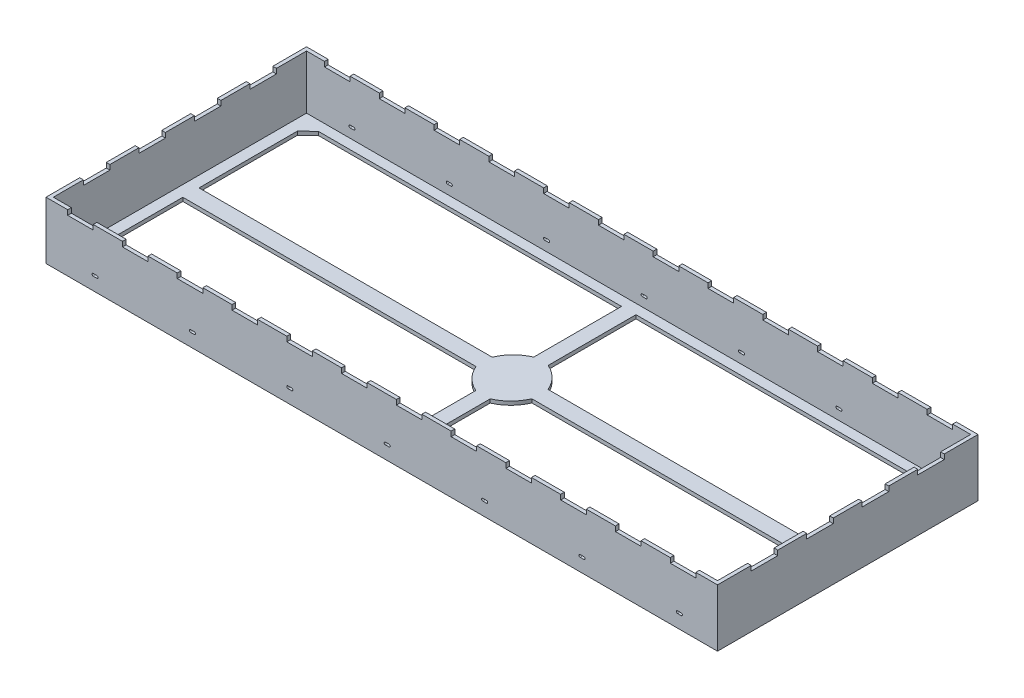
SolidWorks part; units mm, degrees
ref_plane "Front Plane" through (0, 0, 0) normal (0, 0, 1) x (1, 0, 0)
ref_plane "Top Plane" through (0, 0, 0) normal (0, 1, 0) x (1, 0, 0)
ref_plane "Right Plane" through (0, 0, 0) normal (1, 0, 0) x (0, 0, -1)
sketch "Sketch1" plane through (0, 0, 0) normal (0, 1, 0) x (1, 0, 0)
  line L1 (-35.0266, 13.589) -> (35.0266, 13.589)
  line L2 (-35.0266, 13.589) -> (-35.0266, -13.589)
  line L3 (-35.0266, -13.589) -> (35.0266, -13.589)
  line L4 (35.0266, 13.589) -> (35.0266, -13.589)
  line L5 (-35.0266, 13.589) -> (35.0266, -13.589) construction
  line L6 (-35.0266, -13.589) -> (35.0266, 13.589) construction
  point P0 (0, 0)
  dimension "D1" = 70.0532
  dimension "D2" = 27.178
extrude "Boss-Extrude1" add sketch "Sketch1" along normal blind 5.9944
shell "Shell1" thickness 0.381
sketch "Sketch2" plane through (0, 0, 0) normal (0, -1, 0) x (1, 0, 0)
  line L0 (131.1471, 197.1305) -> (804.4804, 197.1305) construction
  line L1 (-32.38, 12.1805) -> (-0.7521, 12.1805)
  line L2 (-0.7521, 12.1805) -> (-0.7521, 3.0227)
  line L3 (-32.38, 12.1805) -> (-33.4968, 11.1083)
  line L4 (-33.4968, 11.1083) -> (-33.4968, 0.844)
  line L5 (-33.4968, 0.844) -> (-2.9133, 0.844)
  line L6 (0, 13.589) -> (0, -13.589) construction
  line L7 (-35.0266, 13.589) -> (35.0266, 13.589) construction
  line L8 (35.0266, -13.589) -> (-35.0266, -13.589) construction
  line L9 (33.4968, 0.844) -> (2.9133, 0.844)
  line L10 (33.4968, 11.1083) -> (33.4968, 0.844)
  line L11 (32.38, 12.1805) -> (33.4968, 11.1083)
  line L12 (0.7521, 12.1805) -> (0.7521, 3.0227)
  line L13 (32.38, 12.1805) -> (0.7521, 12.1805)
  line L14 (-35.0266, 0) -> (35.0266, 0) construction
  line L15 (-35.0266, -13.589) -> (-35.0266, 13.589) construction
  line L16 (35.0266, 13.589) -> (35.0266, -13.589) construction
  line L17 (32.38, -12.1805) -> (0.7521, -12.1805)
  line L18 (0.7521, -12.1805) -> (0.7521, -3.0227)
  line L19 (32.38, -12.1805) -> (33.4968, -11.1083)
  line L20 (33.4968, -11.1083) -> (33.4968, -0.844)
  line L21 (33.4968, -0.844) -> (2.9133, -0.844)
  line L22 (-33.4968, -0.844) -> (-2.9133, -0.844)
  line L23 (-33.4968, -11.1083) -> (-33.4968, -0.844)
  line L24 (-32.38, -12.1805) -> (-33.4968, -11.1083)
  line L25 (-0.7521, -12.1805) -> (-0.7521, -3.0227)
  line L26 (-32.38, -12.1805) -> (-0.7521, -12.1805)
  arc A0 (-0.7521, 3.0227) -> (-2.9133, 0.844) centre (0.9215, -0.7987) ccw
  arc A1 (0.7521, 3.0227) -> (2.9133, 0.844) centre (-0.9215, -0.7987) cw
  arc A2 (0.7521, -3.0227) -> (2.9133, -0.844) centre (-0.9215, 0.7987) ccw
  arc A3 (-0.7521, -3.0227) -> (-2.9133, -0.844) centre (0.9215, 0.7987) cw
extrude "Cut-Extrude1" cut sketch "Sketch2" against normal through all
sketch "Sketch3" plane through (0, 0, -13.589) normal (0, 0, -1) x (-1, 0, 0)
  line L0 (-35.0266, 5.9944) -> (35.0266, 5.9944) construction
  line L1 (-32.766, 6.8594) -> (-30.099, 6.8594)
  line L2 (-32.766, 6.8594) -> (-32.766, 5.4864)
  line L3 (-32.766, 5.4864) -> (-30.099, 5.4864)
  line L4 (-30.099, 6.8594) -> (-30.099, 5.4864)
  line L6 (-27.051, 6.8594) -> (-24.384, 6.8594)
  line L7 (-27.051, 6.8594) -> (-27.051, 5.4864)
  line L8 (-27.051, 5.4864) -> (-24.384, 5.4864)
  line L9 (-24.384, 6.8594) -> (-24.384, 5.4864)
  line L10 (-21.336, 6.8594) -> (-18.669, 6.8594)
  line L11 (-21.336, 6.8594) -> (-21.336, 5.4864)
  line L12 (-21.336, 5.4864) -> (-18.669, 5.4864)
  line L13 (-18.669, 6.8594) -> (-18.669, 5.4864)
  line L14 (-15.621, 6.8594) -> (-12.954, 6.8594)
  line L15 (-15.621, 6.8594) -> (-15.621, 5.4864)
  line L16 (-15.621, 5.4864) -> (-12.954, 5.4864)
  line L17 (-12.954, 6.8594) -> (-12.954, 5.4864)
  line L18 (-9.906, 6.8594) -> (-7.239, 6.8594)
  line L19 (-9.906, 6.8594) -> (-9.906, 5.4864)
  line L20 (-9.906, 5.4864) -> (-7.239, 5.4864)
  line L21 (-7.239, 6.8594) -> (-7.239, 5.4864)
  line L22 (-4.191, 6.8594) -> (-1.524, 6.8594)
  line L23 (-4.191, 6.8594) -> (-4.191, 5.4864)
  line L24 (-4.191, 5.4864) -> (-1.524, 5.4864)
  line L25 (-1.524, 6.8594) -> (-1.524, 5.4864)
  line L26 (1.524, 6.8594) -> (4.191, 6.8594)
  line L27 (1.524, 6.8594) -> (1.524, 5.4864)
  line L28 (1.524, 5.4864) -> (4.191, 5.4864)
  line L29 (4.191, 6.8594) -> (4.191, 5.4864)
  line L30 (7.239, 6.8594) -> (9.906, 6.8594)
  line L31 (7.239, 6.8594) -> (7.239, 5.4864)
  line L32 (7.239, 5.4864) -> (9.906, 5.4864)
  line L33 (9.906, 6.8594) -> (9.906, 5.4864)
  line L34 (12.954, 6.8594) -> (15.621, 6.8594)
  line L35 (12.954, 6.8594) -> (12.954, 5.4864)
  line L36 (12.954, 5.4864) -> (15.621, 5.4864)
  line L37 (15.621, 6.8594) -> (15.621, 5.4864)
  line L38 (18.669, 6.8594) -> (21.336, 6.8594)
  line L39 (18.669, 6.8594) -> (18.669, 5.4864)
  line L40 (18.669, 5.4864) -> (21.336, 5.4864)
  line L41 (21.336, 6.8594) -> (21.336, 5.4864)
  line L42 (24.384, 6.8594) -> (27.051, 6.8594)
  line L43 (24.384, 6.8594) -> (24.384, 5.4864)
  line L44 (24.384, 5.4864) -> (27.051, 5.4864)
  line L45 (27.051, 6.8594) -> (27.051, 5.4864)
  line L46 (30.099, 6.8594) -> (32.766, 6.8594)
  line L47 (30.099, 6.8594) -> (30.099, 5.4864)
  line L48 (30.099, 5.4864) -> (32.766, 5.4864)
  line L49 (32.766, 6.8594) -> (32.766, 5.4864)
  line L50 (-32.766, 6.8594) -> (-27.051, 6.8594) construction
  line L53 (-35.0266, 5.9944) -> (-32.766, 6.8594) construction
  line L54 (32.766, 6.8594) -> (35.0266, 5.9944) construction
  dimension "D1" = 2.667
  dimension "D2" = 0.508
  dimension "D5" = 3.048
  dimension "D4" = 12
extrude "Cut-Extrude2" cut sketch "Sketch3" against normal through all
sketch "Sketch4" plane through (35.0266, 0, 0) normal (1, 0, 0) x (0, 0, -1)
  line L0 (-13.589, 5.9944) -> (13.589, 5.9944) construction
  line L1 (-10.0711, 7.1888) -> (-7.3025, 7.1888)
  line L2 (-10.0711, 7.1888) -> (-10.0711, 5.4864)
  line L3 (-10.0711, 5.4864) -> (-7.3025, 5.4864)
  line L4 (-7.3025, 7.1888) -> (-7.3025, 5.4864)
  line L5 (-4.2799, 7.1888) -> (-1.5113, 7.1888)
  line L6 (-4.2799, 7.1888) -> (-4.2799, 5.4864)
  line L7 (-4.2799, 5.4864) -> (-1.5113, 5.4864)
  line L8 (-1.5113, 7.1888) -> (-1.5113, 5.4864)
  line L9 (1.5113, 7.1888) -> (4.2799, 7.1888)
  line L10 (1.5113, 7.1888) -> (1.5113, 5.4864)
  line L11 (1.5113, 5.4864) -> (4.2799, 5.4864)
  line L12 (4.2799, 7.1888) -> (4.2799, 5.4864)
  line L13 (7.3025, 7.1888) -> (10.0711, 7.1888)
  line L14 (7.3025, 7.1888) -> (7.3025, 5.4864)
  line L15 (7.3025, 5.4864) -> (10.0711, 5.4864)
  line L16 (10.0711, 7.1888) -> (10.0711, 5.4864)
  line L17 (-10.0711, 7.1888) -> (-4.2799, 7.1888) construction
  line L18 (-10.0711, 7.1888) -> (-13.589, 5.9944) construction
  line L19 (10.0711, 7.1888) -> (13.589, 5.9944) construction
  line L20 (13.589, 5.9944) -> (13.589, 0) construction
  dimension "D1" = 2.7686
  dimension "D2" = 0.508
  dimension "D4" = 3.0226
  dimension "D3" = 4
extrude "Cut-Extrude3" cut sketch "Sketch4" against normal through all
sketch "Sketch5" plane through (0, 0, -13.589) normal (0, 0, -1) x (-1, 0, 0)
  line L0 (-31.242, 1.4478) -> (-30.861, 1.4478) construction
  line L1 (-31.242, 1.5748) -> (-30.861, 1.5748)
  line L2 (-31.242, 1.3208) -> (-30.861, 1.3208)
  line L4 (-35.0266, 0) -> (35.0266, 0) construction
  line L5 (-21.082, 1.4478) -> (-20.701, 1.4478) construction
  line L6 (-21.082, 1.5748) -> (-20.701, 1.5748)
  line L7 (-21.082, 1.3208) -> (-20.701, 1.3208)
  line L8 (-10.922, 1.4478) -> (-10.541, 1.4478) construction
  line L9 (-10.922, 1.5748) -> (-10.541, 1.5748)
  line L10 (-10.922, 1.3208) -> (-10.541, 1.3208)
  line L11 (-0.762, 1.4478) -> (-0.381, 1.4478) construction
  line L12 (-0.762, 1.5748) -> (-0.381, 1.5748)
  line L13 (-0.762, 1.3208) -> (-0.381, 1.3208)
  line L14 (9.398, 1.4478) -> (9.779, 1.4478) construction
  line L15 (9.398, 1.5748) -> (9.779, 1.5748)
  line L16 (9.398, 1.3208) -> (9.779, 1.3208)
  line L17 (19.558, 1.4478) -> (19.939, 1.4478) construction
  line L18 (19.558, 1.5748) -> (19.939, 1.5748)
  line L19 (19.558, 1.3208) -> (19.939, 1.3208)
  line L20 (29.718, 1.4478) -> (30.099, 1.4478) construction
  line L21 (29.718, 1.5748) -> (30.099, 1.5748)
  line L22 (29.718, 1.3208) -> (30.099, 1.3208)
  line L23 (-31.242, 1.4478) -> (-21.082, 1.4478) construction
  line L24 (-35.0266, 5.9944) -> (-35.0266, 0) construction
  arc A0 (-31.242, 1.5748) -> (-31.242, 1.3208) centre (-31.242, 1.4478) ccw
  arc A1 (-30.861, 1.3208) -> (-30.861, 1.5748) centre (-30.861, 1.4478) ccw
  arc A2 (-21.082, 1.5748) -> (-21.082, 1.3208) centre (-21.082, 1.4478) ccw
  arc A3 (-20.701, 1.3208) -> (-20.701, 1.5748) centre (-20.701, 1.4478) ccw
  arc A4 (-10.922, 1.5748) -> (-10.922, 1.3208) centre (-10.922, 1.4478) ccw
  arc A5 (-10.541, 1.3208) -> (-10.541, 1.5748) centre (-10.541, 1.4478) ccw
  arc A6 (-0.762, 1.5748) -> (-0.762, 1.3208) centre (-0.762, 1.4478) ccw
  arc A7 (-0.381, 1.3208) -> (-0.381, 1.5748) centre (-0.381, 1.4478) ccw
  arc A8 (9.398, 1.5748) -> (9.398, 1.3208) centre (9.398, 1.4478) ccw
  arc A9 (9.779, 1.3208) -> (9.779, 1.5748) centre (9.779, 1.4478) ccw
  arc A10 (19.558, 1.5748) -> (19.558, 1.3208) centre (19.558, 1.4478) ccw
  arc A11 (19.939, 1.3208) -> (19.939, 1.5748) centre (19.939, 1.4478) ccw
  arc A12 (29.718, 1.5748) -> (29.718, 1.3208) centre (29.718, 1.4478) ccw
  arc A13 (30.099, 1.3208) -> (30.099, 1.5748) centre (30.099, 1.4478) ccw
  point P2 (-31.0515, 1.4478)
  point P12 (-20.8915, 1.4478)
  point P19 (-10.7315, 1.4478)
  point P26 (-0.5715, 1.4478)
  point P33 (9.5885, 1.4478)
  point P40 (19.7485, 1.4478)
  point P47 (29.9085, 1.4478)
  dimension "D5" = 10.16
  dimension "D6" = 3.6576
  dimension "D1" = 0.254
  dimension "D2" = 0.381
  dimension "D3" = 1.3208
  dimension "D4" = 7
extrude "Cut-Extrude4" cut sketch "Sketch5" against normal through all
